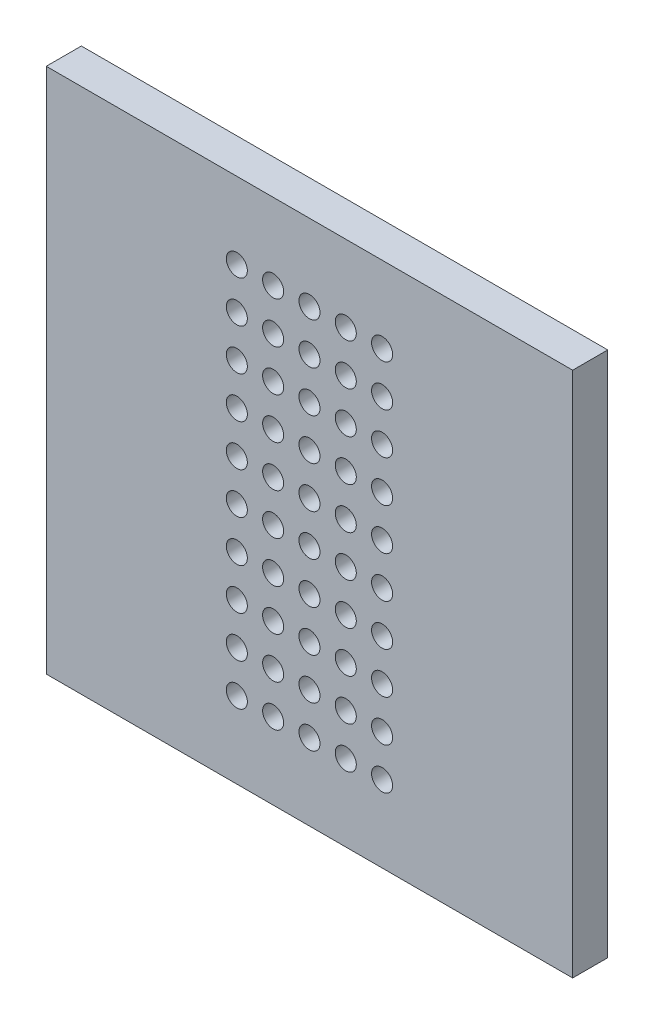
SolidWorks part; units mm, degrees
ref_plane "Plan de face" through (0, 0, 0) normal (0, 0, 1) x (1, 0, 0)
ref_plane "Plan de dessus" through (0, 0, 0) normal (0, 1, 0) x (1, 0, 0)
ref_plane "Plan de droite" through (0, 0, 0) normal (1, 0, 0) x (0, 0, -1)
sketch "Esquisse1" plane through (0, 0, 0) normal (0, 0, 1) x (1, 0, 0)
  line L1 (-15, -15) -> (15, -15)
  line L2 (-15, -15) -> (-15, 15)
  line L3 (-15, 15) -> (15, 15)
  line L4 (15, -15) -> (15, 15)
  line L5 (-15, -15) -> (15, 15) construction
  line L6 (-15, 15) -> (15, -15) construction
  point P0 (0, 0)
extrude "Base_Plate" add sketch "Esquisse1" along normal blind 2
sketch "Sketch_Perforations" plane through (0, 0, 2) normal (0, 0, 1) x (1, 0, 0)
  circle A0 centre (-4.14, -10.64) radius 0.6
  circle A1 centre (-4.14, -8.27) radius 0.6
  circle A2 centre (-4.14, -5.91) radius 0.6
  circle A3 centre (-4.14, -3.55) radius 0.6
  circle A4 centre (-4.14, -1.18) radius 0.6
  circle A5 centre (-4.14, 1.18) radius 0.6
  circle A6 centre (-4.14, 3.55) radius 0.6
  circle A7 centre (-4.14, 5.91) radius 0.6
  circle A8 centre (-4.14, 8.27) radius 0.6
  circle A9 centre (-4.14, 10.64) radius 0.6
  circle A10 centre (-2.07, -10.64) radius 0.6
  circle A11 centre (-2.07, -8.27) radius 0.6
  circle A12 centre (-2.07, -5.91) radius 0.6
  circle A13 centre (-2.07, -3.55) radius 0.6
  circle A14 centre (-2.07, -1.18) radius 0.6
  circle A15 centre (-2.07, 1.18) radius 0.6
  circle A16 centre (-2.07, 3.55) radius 0.6
  circle A17 centre (-2.07, 5.91) radius 0.6
  circle A18 centre (-2.07, 8.27) radius 0.6
  circle A19 centre (-2.07, 10.64) radius 0.6
  circle A20 centre (0, -10.64) radius 0.6
  circle A21 centre (0, -8.27) radius 0.6
  circle A22 centre (0, -5.91) radius 0.6
  circle A23 centre (0, -3.55) radius 0.6
  circle A24 centre (0, -1.18) radius 0.6
  circle A25 centre (0, 1.18) radius 0.6
  circle A26 centre (0, 3.55) radius 0.6
  circle A27 centre (0, 5.91) radius 0.6
  circle A28 centre (0, 8.27) radius 0.6
  circle A29 centre (0, 10.64) radius 0.6
  circle A30 centre (2.07, -10.64) radius 0.6
  circle A31 centre (2.07, -8.27) radius 0.6
  circle A32 centre (2.07, -5.91) radius 0.6
  circle A33 centre (2.07, -3.55) radius 0.6
  circle A34 centre (2.07, -1.18) radius 0.6
  circle A35 centre (2.07, 1.18) radius 0.6
  circle A36 centre (2.07, 3.55) radius 0.6
  circle A37 centre (2.07, 5.91) radius 0.6
  circle A38 centre (2.07, 8.27) radius 0.6
  circle A39 centre (2.07, 10.64) radius 0.6
  circle A40 centre (4.14, -10.64) radius 0.6
  circle A41 centre (4.14, -8.27) radius 0.6
  circle A42 centre (4.14, -5.91) radius 0.6
  circle A43 centre (4.14, -3.55) radius 0.6
  circle A44 centre (4.14, -1.18) radius 0.6
  circle A45 centre (4.14, 1.18) radius 0.6
  circle A46 centre (4.14, 3.55) radius 0.6
  circle A47 centre (4.14, 5.91) radius 0.6
  circle A48 centre (4.14, 8.27) radius 0.6
  circle A49 centre (4.14, 10.64) radius 0.6
extrude "Cut_Perforations" cut sketch "Sketch_Perforations" against normal blind 10
